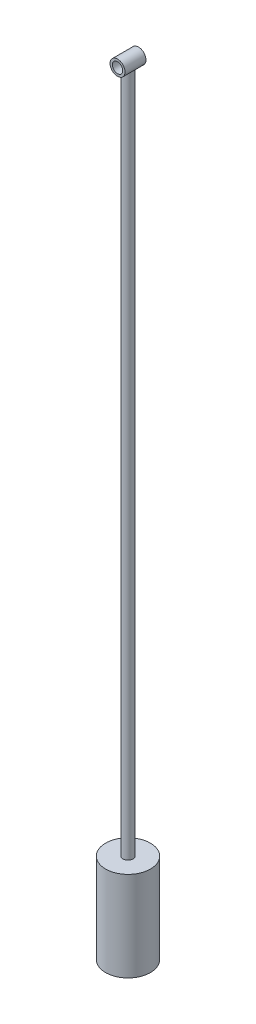
SolidWorks part; units mm, degrees
ref_plane "Front Plane" through (0, 0, 0) normal (0, 0, 1) x (1, 0, 0)
ref_plane "Top Plane" through (0, 0, 0) normal (0, 1, 0) x (1, 0, 0)
ref_plane "Right Plane" through (0, 0, 0) normal (1, 0, 0) x (0, 0, -1)
sketch "Sketch1" plane through (0, 0, 166.9224) normal (0, 0, 1) x (1, 0, 0)
  circle A0 centre (39.892, 76.7003) radius 2.5
  circle A1 centre (39.892, 76.7003) radius 1.7339
  circle A2 centre (39.892, 76.7003) radius 2.5 construction
  circle A3 centre (39.892, 76.7003) radius 1.7339 construction
extrude "Boss-Extrude1" add sketch "Sketch1" against normal blind 7 from offset 7 offset against normal yes
sketch "Sketch2" plane through (0, 36.7003, 0) normal (0, -1, 0) x (1, 0, 0)
  line L0 (39.892, 152.9224) -> (39.892, 159.9224) construction
  line L1 (37.392, 152.9224) -> (42.392, 152.9224) construction
  line L2 (42.392, 159.9224) -> (37.392, 159.9224) construction
  circle A0 centre (39.892, 156.4224) radius 1.6887
extrude "Boss-Extrude2" add sketch "Sketch2" against normal blind 38.25 and the other way blind 200
sketch "Sketch3" plane through (0, -163.2997, 0) normal (0, -1, 0) x (-1, 0, 0)
  circle A0 centre (-39.892, -156.4224) radius 7.5
  dimension "D1" = 15
extrude "Boss-Extrude3" add sketch "Sketch3" against normal blind 30 from offset 20
